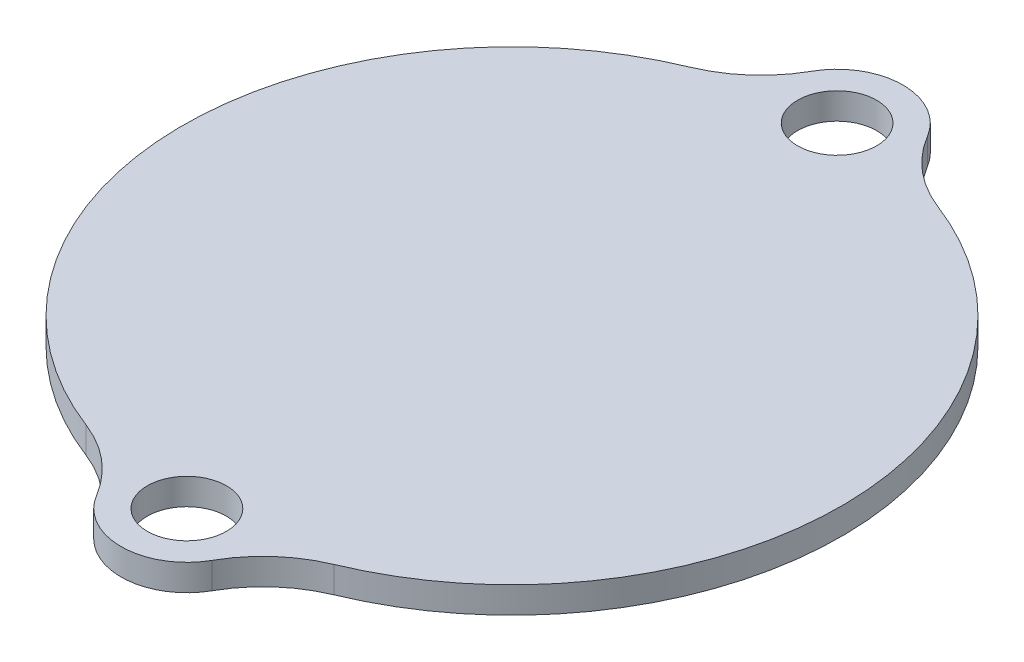
SolidWorks part; units mm, degrees
ref_plane "Front Plane" through (0, 0, 0) normal (0, 0, 1) x (1, 0, 0)
ref_plane "Top Plane" through (0, 0, 0) normal (0, 1, 0) x (1, 0, 0)
ref_plane "Right Plane" through (0, 0, 0) normal (1, 0, 0) x (0, 0, -1)
sketch "Sketch1" plane through (0, 0, 0) normal (0, 1, 0) x (1, 0, 0)
  arc A0 (-9.587, 23.0887) -> (-8.9691, -23.3357) centre (0, 0) ccw
  arc A1 (3.9638, 27.5552) -> (-4.6957, 27.4399) centre (-0.3327, 24.9978) ccw
  arc A2 (-3.9638, -27.5552) -> (4.6957, -27.4399) centre (0.3327, -24.9978) ccw
  arc A3 (9.587, -23.0887) -> (8.9691, 23.3357) centre (0, 0) ccw
  circle A4 centre (-0.3327, 24.9978) radius 3
  circle A5 centre (0.3327, -24.9978) radius 3
  arc A6 (-9.587, 23.0887) -> (-4.6957, 27.4399) centre (-13.4218, 32.3242) ccw
  arc A7 (8.9691, 23.3357) -> (3.9638, 27.5552) centre (12.5567, 32.67) cw
  arc A8 (9.587, -23.0887) -> (4.6957, -27.4399) centre (13.4218, -32.3242) ccw
  arc A9 (-8.9691, -23.3357) -> (-3.9638, -27.5552) centre (-12.5567, -32.67) cw
  point P9 (0, 0)
  point P15 (0, 0)
  point P19 (5.3006, -24.4316)
  dimension "D1" = 50
  dimension "D2" = 10
  dimension "D4" = 6
  dimension "D6" = 10
  dimension "D7" = 10
  dimension "D8" = 10
  dimension "D9" = 10
  dimension "D3" = 2
  dimension "D5" = 2
extrude "Boss-Extrude1" add sketch "Sketch1" along normal blind 2
